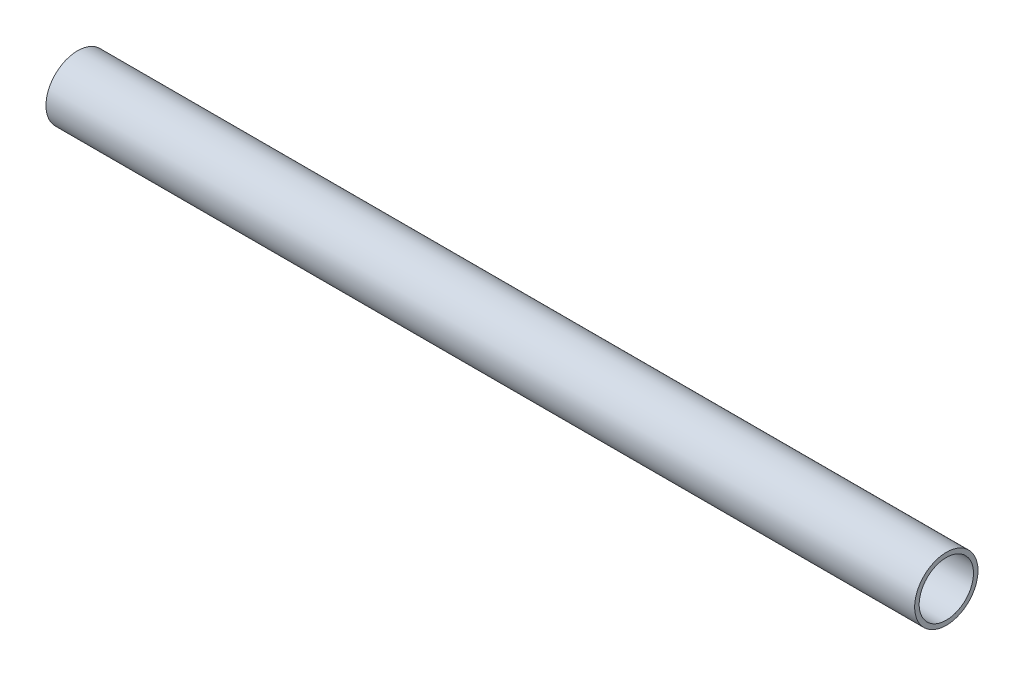
SolidWorks part; units mm, degrees
ref_plane "Front Plane" through (0, 0, 0) normal (0, 0, 1) x (1, 0, 0)
ref_plane "Top Plane" through (0, 0, 0) normal (0, 1, 0) x (1, 0, 0)
ref_plane "Right Plane" through (0, 0, 0) normal (1, 0, 0) x (0, 0, -1)
sketch "Sketch1" plane through (0, 0, 0) normal (1, 0, 0) x (0, 0, -1)
  circle A0 centre (0, 0) radius 44.45
  circle A1 centre (0, 0) radius 38.1
  dimension "D1" = 88.9
  dimension "D2" = 76.2
extrude "Boss-Extrude1" add sketch "Sketch1" along normal mid plane 1219.2
